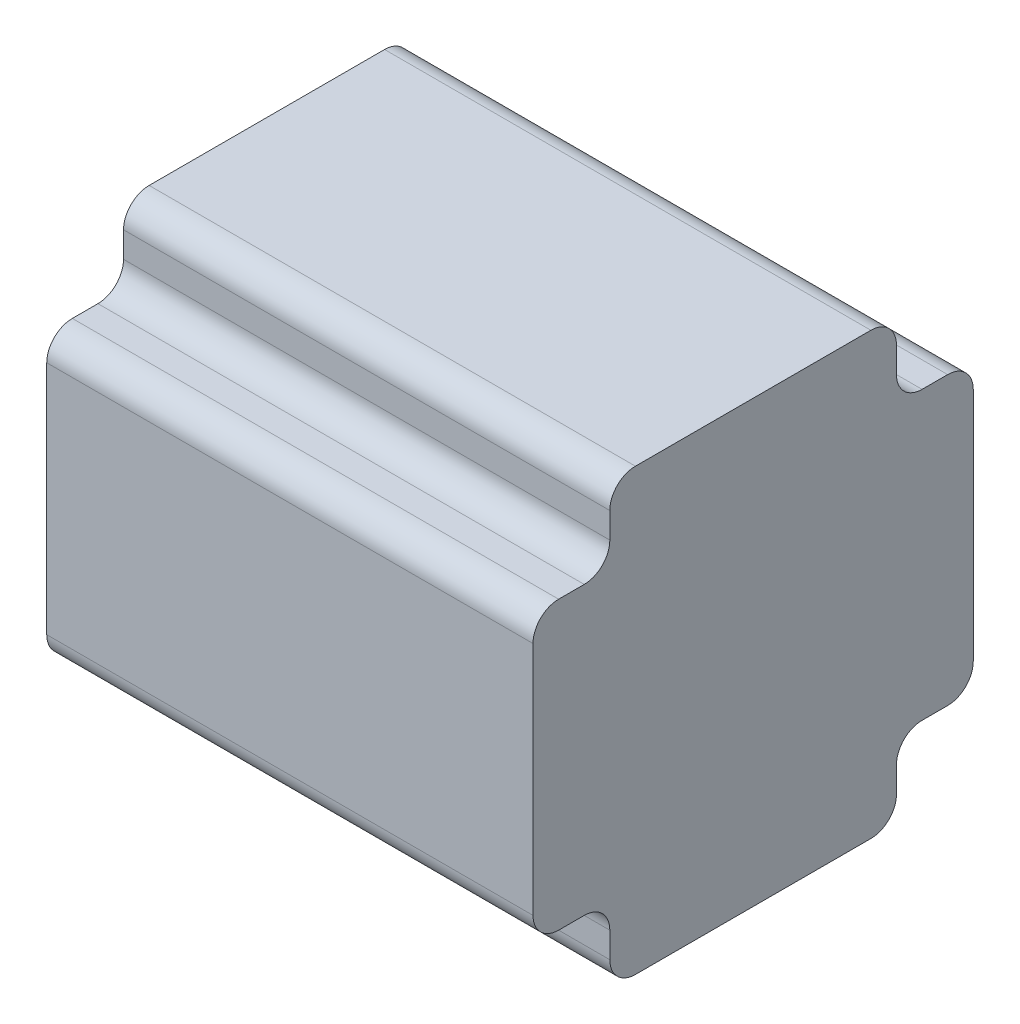
SolidWorks part; units mm, degrees
ref_plane "Front Plane" through (0, 0, 0) normal (0, 0, 1) x (1, 0, 0)
ref_plane "Top Plane" through (0, 0, 0) normal (0, 1, 0) x (1, 0, 0)
ref_plane "Right Plane" through (0, 0, 0) normal (1, 0, 0) x (0, 0, -1)
sketch "Sketch1" plane through (0, 0, 0) normal (1, 0, 0) x (0, 0, -1)
  line L0 (15, 81) -> (15, 76)
  line L1 (20, 0) -> (66, 0)
  line L2 (0, 20) -> (0, 66)
  line L3 (20, 86) -> (66, 86)
  line L4 (86, 20) -> (86, 66)
  line L5 (10, 71) -> (5, 71)
  line L6 (43, 86) -> (43, 0) construction
  line L7 (63.558, 43) -> (-22.442, 43) construction
  line L8 (15, 5) -> (15, 10)
  line L9 (10, 15) -> (5, 15)
  line L10 (76, 15) -> (81, 15)
  line L11 (71, 5) -> (71, 10)
  line L12 (76, 71) -> (81, 71)
  line L13 (71, 81) -> (71, 76)
  arc A0 (81, 15) -> (86, 20) centre (81, 20) ccw
  arc A1 (76, 15) -> (71, 10) centre (76, 10) ccw
  arc A2 (71, 5) -> (66, 0) centre (66, 5) cw
  arc A3 (15, 5) -> (20, 0) centre (20, 5) ccw
  arc A4 (15, 10) -> (10, 15) centre (10, 10) ccw
  arc A5 (5, 15) -> (0, 20) centre (5, 20) cw
  arc A6 (81, 71) -> (86, 66) centre (81, 66) cw
  arc A7 (76, 71) -> (71, 76) centre (76, 76) cw
  arc A8 (71, 81) -> (66, 86) centre (66, 81) ccw
  arc A9 (15, 81) -> (20, 86) centre (20, 81) cw
  arc A10 (15, 76) -> (10, 71) centre (10, 76) cw
  arc A11 (5, 71) -> (0, 66) centre (5, 66) ccw
  point P3 (86, 15)
  point P23 (71, 15)
  point P26 (71, 0)
  point P29 (15, 0)
  point P32 (15, 15)
  point P35 (0, 15)
  point P38 (86, 71)
  point P41 (71, 71)
  point P44 (71, 86)
  point P47 (15, 86)
  point P50 (15, 71)
  point P53 (0, 71)
  dimension "D3" = 5
  dimension "D1" = 56
  dimension "D2" = 15
extrude "Boss-Extrude1" add sketch "Sketch1" along normal blind 95
